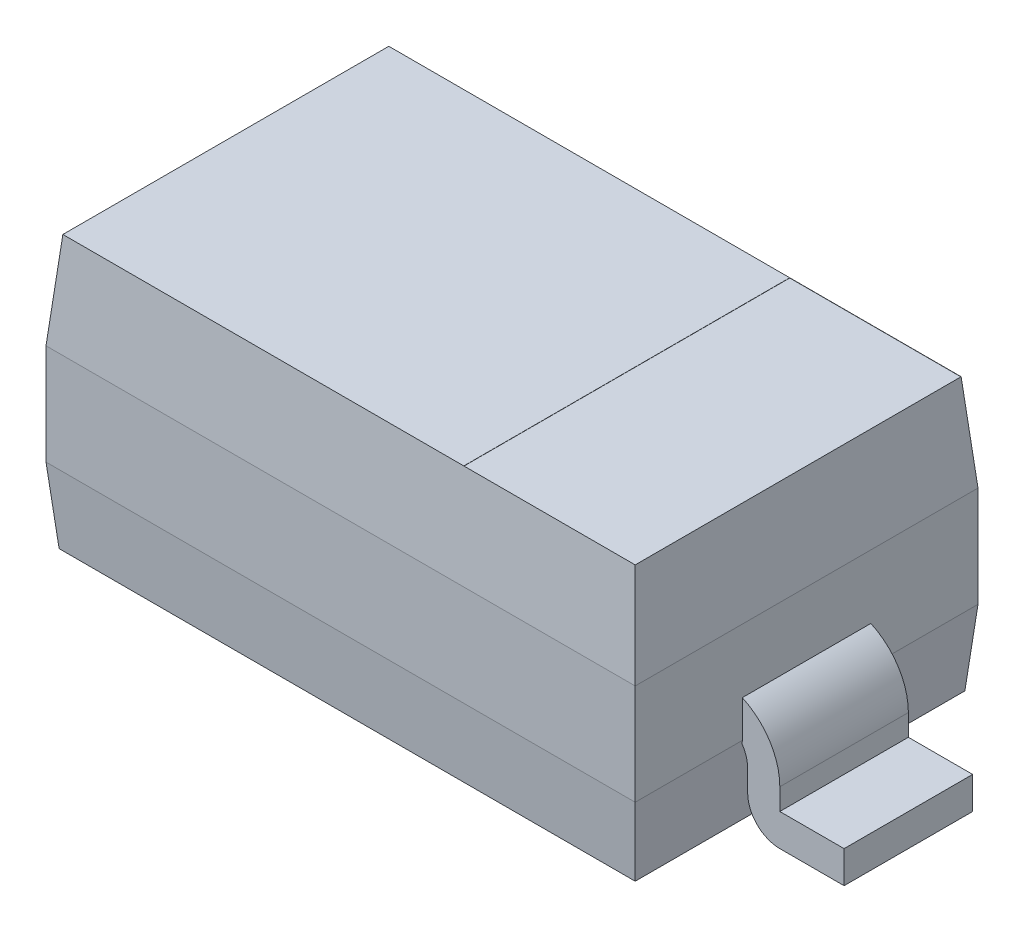
SolidWorks part; units mm, degrees
ref_plane "Front Plane" through (0, 0, 0) normal (0, 0, 1) x (1, 0, 0)
ref_plane "Top Plane" through (0, 0, 0) normal (0, 1, 0) x (1, 0, 0)
ref_plane "Right Plane" through (0, 0, 0) normal (1, 0, 0) x (0, 0, -1)
sketch "Sketch1" plane through (0, 0, 0) normal (0, 1, 0) x (1, 0, 0)
  line L4 (0, 0) -> (1.375, 0) construction
  line L5 (-1.375, 0.8) -> (1.375, 0.8)
  line L6 (-1.375, 0.8) -> (-1.375, -0.8)
  line L7 (-1.375, -0.8) -> (1.375, -0.8)
  line L8 (1.375, 0.8) -> (1.375, -0.8)
  line L9 (0, 0) -> (0, 0.8) construction
  dimension "D1" = 2.75
  dimension "D2" = 1.6
extrude "Base-Extrude" add sketch "Sketch1" along normal blind 1.27
chamfer "Chamfer1" distance 0.45 angle 5 4 edges at (1.375, 1.27, 0) (0, 1.27, -0.8) (-1.375, 1.27, 0) (0, 1.27, 0.8)
chamfer "Chamfer3" distance 0.35 angle 5 4 edges at (0, 0, -0.8) (1.375, 0, 0) (0, 0, 0.8) (-1.375, 0, 0)
sketch "Sketch2" plane through (0, 0, 0) normal (0, 0, 1) x (1, 0, 0)
  line L0 (-1.25, 0.4) -> (1.25, 0.4)
  line L1 (1.4, 0.25) -> (1.4, 0.15)
  line L2 (1.55, 0) -> (1.85, 0)
  line L3 (-1.4, 0.25) -> (-1.4, 0.15)
  line L4 (-1.55, 0) -> (-1.85, 0)
  line L5 (1.3444, 0) -> (-1.3444, 0) construction
  line L6 (0, 0) -> (0, 0.4) construction
  arc A0 (-1.4, 0.15) -> (-1.55, 0) centre (-1.55, 0.15) cw
  arc A1 (-1.25, 0.4) -> (-1.4, 0.25) centre (-1.25, 0.25) ccw
  arc A2 (1.4, 0.25) -> (1.25, 0.4) centre (1.25, 0.25) ccw
  arc A3 (1.55, 0) -> (1.4, 0.15) centre (1.55, 0.15) cw
  point P15 (-1.4, 0.4)
  point P18 (1.4, 0.4)
  dimension "D4" = 0.15
  dimension "D1" = 0.4
  dimension "D2" = 3.7
  dimension "D3" = 2.8
extrude "Boss-Extrude-Thin2" add sketch "Sketch2" along normal blind 0.3 and the other way blind 0.3 thin
sketch "Sketch3" plane through (0, 1.27, 0) normal (0, 1, 0) x (-1, 0, 0)
  line L0 (-1.3356, -0.7606) -> (1.3356, -0.7606) construction
  line L1 (-0.5356, 0.7606) -> (-1.3356, 0.7606)
  line L2 (-0.5356, 0.7606) -> (-0.5356, -0.7606)
  line L3 (-0.5356, -0.7606) -> (-1.3356, -0.7606)
  line L4 (-1.3356, 0.7606) -> (-1.3356, -0.7606)
  dimension "D1" = 0.8
extrude "Cut-Extrude1" cut sketch "Sketch3" against normal blind 0.001
sketch "Component_Outline" plane through (0, 0, 0) normal (0, 1, 0) x (1, 0, 0)
  line L0 (1.85, 0.3) -> (1.375, 0.3)
  line L1 (1.375, 0.3) -> (1.375, 0.8)
  line L2 (1.375, 0.8) -> (-1.375, 0.8)
  line L3 (-1.375, 0.8) -> (-1.375, 0.3)
  line L4 (-1.375, 0.3) -> (-1.85, 0.3)
  line L5 (-1.85, 0.3) -> (-1.85, -0.3)
  line L6 (-1.85, -0.3) -> (-1.375, -0.3)
  line L7 (-1.375, -0.3) -> (-1.375, -0.8)
  line L8 (-1.375, -0.8) -> (1.375, -0.8)
  line L9 (1.375, -0.8) -> (1.375, -0.3)
  line L10 (1.375, -0.3) -> (1.85, -0.3)
  line L11 (1.85, -0.3) -> (1.85, 0.3)
